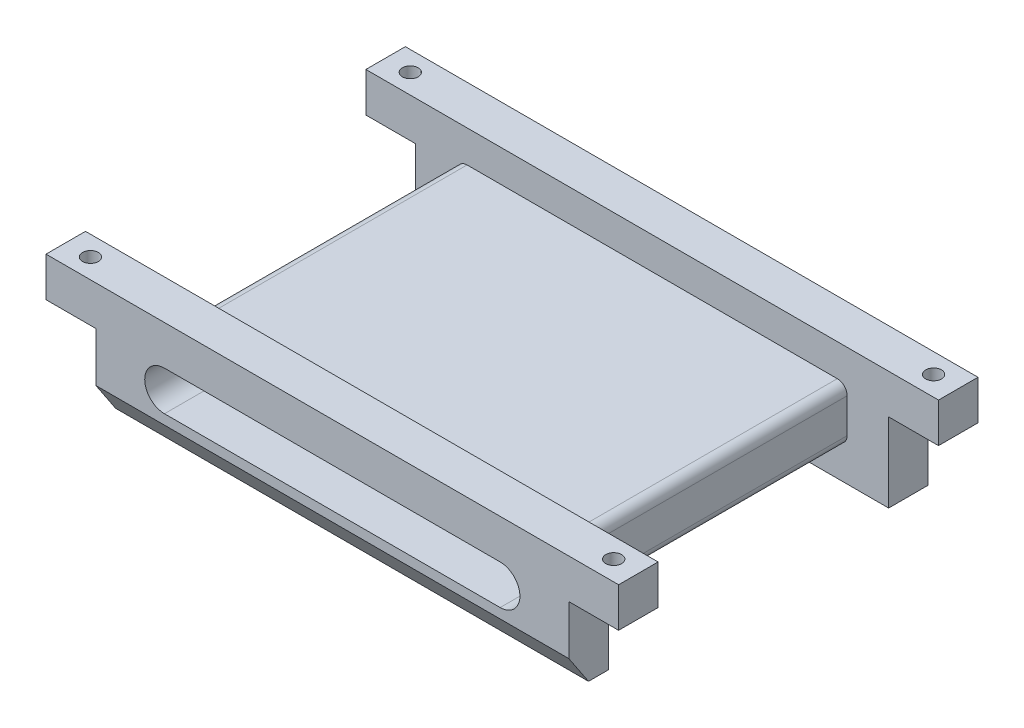
SolidWorks part; units mm, degrees
ref_plane "Front Plane" through (0, 0, 0) normal (0, 0, 1) x (1, 0, 0)
ref_plane "Top Plane" through (0, 0, 0) normal (0, 1, 0) x (1, 0, 0)
ref_plane "Right Plane" through (0, 0, 0) normal (1, 0, 0) x (0, 0, -1)
sketch "Sketch1" plane through (0, 0, 0) normal (0, 0, 1) x (1, 0, 0)
  line L0 (0, 12) -> (58, 12)
  line L1 (58, 12) -> (58, 8)
  line L2 (58, 8) -> (52.95, 8)
  line L3 (52.95, 8) -> (52.95, 0)
  line L4 (52.95, 0) -> (5.05, 0)
  line L5 (5.05, 0) -> (5.05, 8)
  line L6 (5.05, 8) -> (0, 8)
  line L7 (0, 8) -> (0, 12)
  line L8 (12, 6) -> (46, 6) construction
  line L9 (12, 8) -> (46, 8)
  line L10 (12, 4) -> (46, 4)
  arc A0 (12, 8) -> (12, 4) centre (12, 6) ccw
  arc A1 (46, 4) -> (46, 8) centre (46, 6) ccw
  point P11 (29, 6)
  dimension "D1" = 8
  dimension "D2" = 4
  dimension "D3" = 47.9
  dimension "D4" = 34
  dimension "D5" = 6.95
  dimension "D6" = 58
  dimension "D7" = 4
  dimension "D8" = 4
extrude "Boss-Extrude1" add sketch "Sketch1" along normal blind 36.4
sketch "Sketch2" plane through (0, 0, 36.4) normal (0, 0, 1) x (1, 0, 0)
  line L0 (5.05, 8) -> (5.05, 0) construction
  line L1 (10.25, 8.75) -> (47.75, 8.75)
  line L2 (9.25, 7.75) -> (9.25, 4.25)
  line L3 (10.25, 3.25) -> (47.75, 3.25)
  line L4 (48.75, 7.75) -> (48.75, 4.25)
  line L6 (12, 4) -> (46, 4) construction
  arc A0 (9.25, 4.25) -> (10.25, 3.25) centre (10.25, 4.25) ccw
  arc A1 (47.75, 3.25) -> (48.75, 4.25) centre (47.75, 4.25) ccw
  arc A2 (47.75, 8.75) -> (48.75, 7.75) centre (47.75, 7.75) cw
  arc A3 (10.25, 8.75) -> (9.25, 7.75) centre (10.25, 7.75) ccw
  dimension "D1" = 1
  dimension "D2" = 5.5
  dimension "D3" = 4.2
  dimension "D4" = 39.5
  dimension "D5" = 0.75
extrude "Cut-Extrude1" cut sketch "Sketch2" against normal offset from surface (28.4 mm away) 4 from offset 4 flip side to cut up to face at (29, 7, 0) offset against normal yes
chamfer "Chamfer1" distance 2 distance2 3 1 edges at (29, 0, 36.4)
hole_wizard "Tap Drill for M2x0.4 Tap1" positions "Sketch4" profile "Sketch3" hole size "M2x0.4" standard "ANSI Metric" end condition up to next
sketch "Sketch4" plane through (0, 12, 0) normal (0, 1, 0) x (1, 0, 0)
  line L0 (58, -36.4) -> (0, -36.4) construction
  line L1 (0, -36.4) -> (0, -32.4) construction
  line L2 (0, -4) -> (58, -4) construction
  line L3 (58, -4) -> (58, 0) construction
  point P0 (2.5, -2)
  point P2 (55.5, -2)
  point P4 (55.5, -34.4)
  point P6 (2.5, -34.4)
  dimension "D1" = 2
  dimension "D2" = 2.5
  dimension "D3" = 2
  dimension "D4" = 2.5
sketch "Sketch3" plane through (2.5, 12, 2) normal (1, 0, 0) x (0, 0, 1)
  line L0 (0, 0) -> (0, 4)
  line L1 (0, 4) -> (0.8, 4)
  line L2 (0.8, 4) -> (0.8, 0)
  line L5 (0.8, 0) -> (0, 0)
  line L11 (0, -6.35) -> (0, 107.95) construction
  dimension "Thru Hole Dia." = 1.6
  dimension "Thru Hole Depth" = 4
